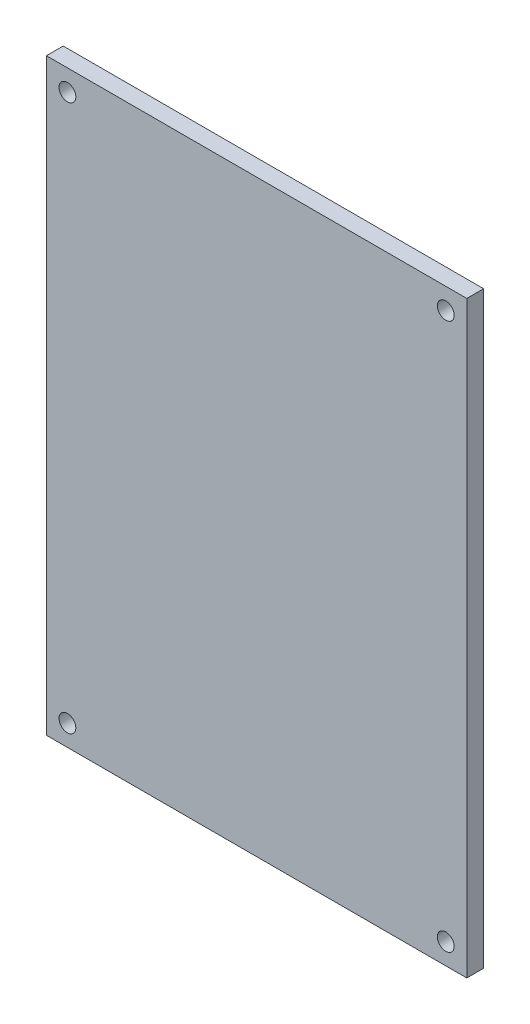
SolidWorks part; units mm, degrees
material "ABS"
ref_plane "前视基准面" through (0, 0, 0) normal (0, 0, 1) x (1, 0, 0)
ref_plane "上视基准面" through (0, 0, 0) normal (0, 1, 0) x (1, 0, 0)
ref_plane "右视基准面" through (0, 0, 0) normal (1, 0, 0) x (0, 0, -1)
sketch "草图1" plane through (0, 0, 0) normal (0, 0, 1) x (1, 0, 0)
  line L0 (0, 0) -> (0, 10) construction
  line L1 (-25, 35) -> (25, 35)
  line L2 (-25, 35) -> (-25, -35)
  line L3 (-25, -35) -> (25, -35)
  line L4 (25, 35) -> (25, -35)
  line L5 (-25, 35) -> (25, -35) construction
  line L6 (-25, -35) -> (25, 35) construction
  line L7 (0, 0) -> (10, 0) construction
  line L8 (-25, 35) -> (-25, 32.5) construction
  line L9 (-25, 32.5) -> (-22.5, 32.5) construction
  circle A0 centre (-22.5, 32.5) radius 1
  circle A1 centre (22.5, 32.5) radius 1
  circle A2 centre (22.5, -32.5) radius 1
  circle A3 centre (-22.5, -32.5) radius 1
  point P0 (0, 0)
  dimension "D1" = 50
  dimension "D3" = 2
  dimension "D5" = 2.5
  dimension "D2" = 70
  dimension "D4" = 2.5
extrude "凸台-拉伸1" add sketch "草图1" along normal blind 2
sketch "草图2" plane through (0, 0, 0) normal (0, 0, -1) x (-1, 0, 0)
  line L0 (25, -35) -> (25, -6.5) construction
  line L1 (25, 35) -> (25, -35) construction
  line L2 (25, -6.5) -> (12.5, -6.5) construction
  line L3 (12.5, -6.5) -> (12.5, 18.5)
  line L4 (12.5, -6.5) -> (-12.5, -6.5)
  line L5 (-12.5, -6.5) -> (-12.5, 18.5)
  line L6 (-12.5, 18.5) -> (12.5, 18.5)
  dimension "D1" = 28.5
  dimension "D2" = 25
  dimension "D3" = 12.5
